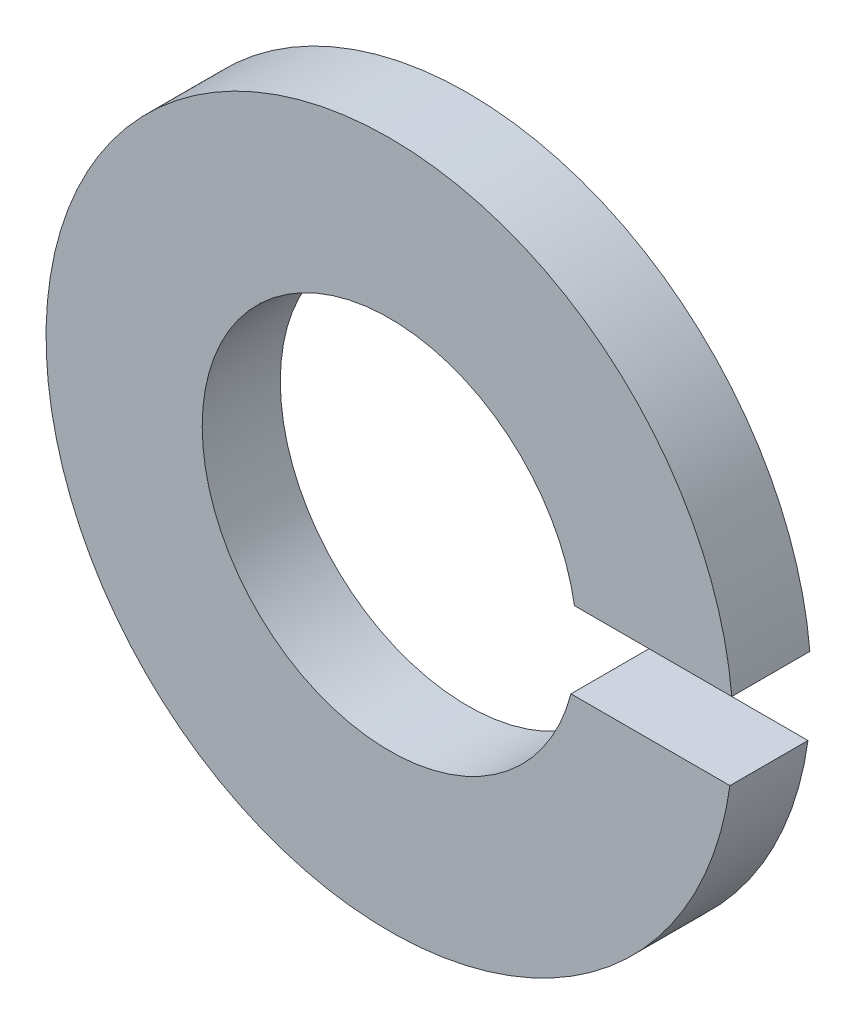
SolidWorks part; units mm, degrees
material "AISI Type A2 Tool Steel"
ref_plane "Front" through (0, 0, 0) normal (0, 0, 1) x (1, 0, 0)
ref_plane "Top" through (0, 0, 0) normal (0, 1, 0) x (1, 0, 0)
ref_plane "Right" through (0, 0, 0) normal (1, 0, 0) x (0, 0, -1)
sketch "Sketch1" plane through (0, 0, 0) normal (0, 0, 1) x (1, 0, 0)
  line L0 (3.3223, -0.3022) -> (0.5645, -0.3022)
  line L1 (3.3223, -0.3022) -> (3.3223, 0.1978)
  line L2 (0.5645, -0.3022) -> (0.5645, 0.1978)
  line L3 (3.3223, 0.1978) -> (0.5645, 0.1978)
  line L4 (3.3223, -0.3022) -> (0.5645, 0.1978) construction
  line L5 (0.5645, -0.3022) -> (3.3223, 0.1978) construction
  arc A0 (2.1911, 0.1978) -> (2.1791, -0.3022) centre (0, 0) ccw
  arc A1 (1.1836, 0.1978) -> (1.1613, -0.3022) centre (0, 0) ccw
  point P5 (1.9434, -0.0522)
  dimension "D1" = 4.4
  dimension "D2" = 2.4
  dimension "D3" = 0.5
extrude "Boss-Extrude1" add sketch "Sketch1" along normal blind 0.5 contours A1 L3 A0 L0
